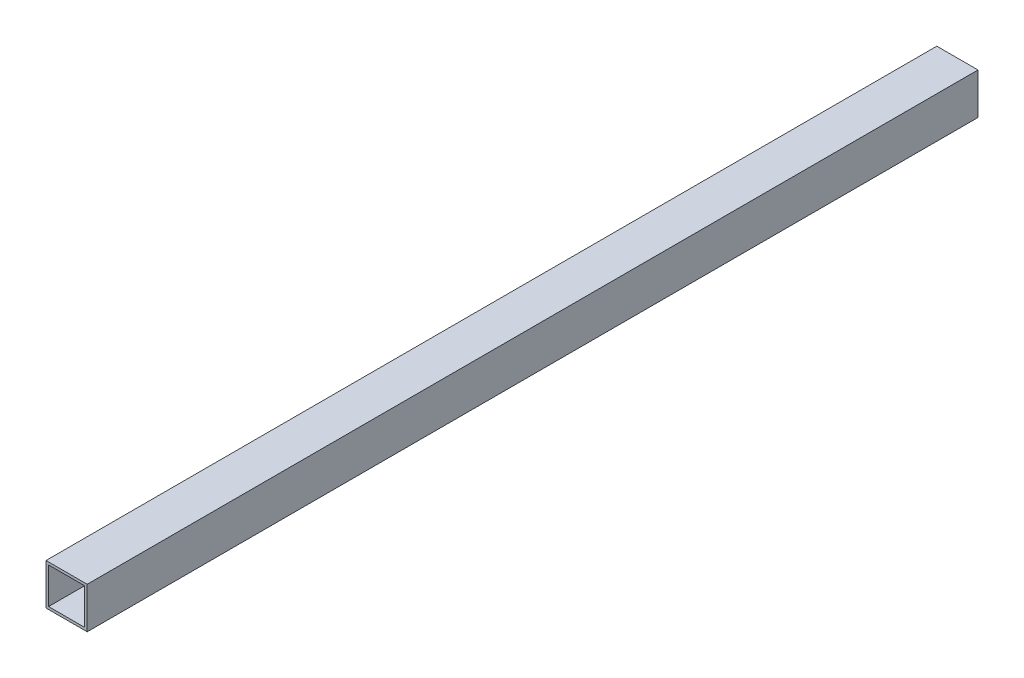
SolidWorks part; units mm, degrees
material "6061 Alloy"
ref_plane "Front Plane" through (0, 0, 0) normal (0, 0, 1) x (1, 0, 0)
ref_plane "Top Plane" through (0, 0, 0) normal (0, 1, 0) x (1, 0, 0)
ref_plane "Right Plane" through (0, 0, 0) normal (1, 0, 0) x (0, 0, -1)
sketch "Sketch1" plane through (0, 0, 0) normal (0, 0, 1) x (1, 0, 0)
  line L0 (-25.4, -419.1) -> (-25.4, 419.1) construction
  line L1 (25.4, -25.4) -> (-25.4, -25.4)
  line L2 (25.4, -25.4) -> (25.4, 25.4)
  line L3 (25.4, 25.4) -> (-25.4, 25.4)
  line L4 (-25.4, -25.4) -> (-25.4, 25.4)
  line L5 (25.4, -25.4) -> (-25.4, 25.4) construction
  line L6 (25.4, 25.4) -> (-25.4, -25.4) construction
  line L7 (22.225, -22.225) -> (22.225, 22.225)
  line L8 (22.225, 22.225) -> (-22.225, 22.225)
  line L9 (-22.225, -22.225) -> (-22.225, 22.225)
  line L10 (22.225, -22.225) -> (-22.225, -22.225)
  point P0 (0, 0)
  dimension "D1" = 50.8
  dimension "D2" = 3.175
extrude "Boss-Extrude1" add sketch "Sketch1" along normal blind 1098.55
